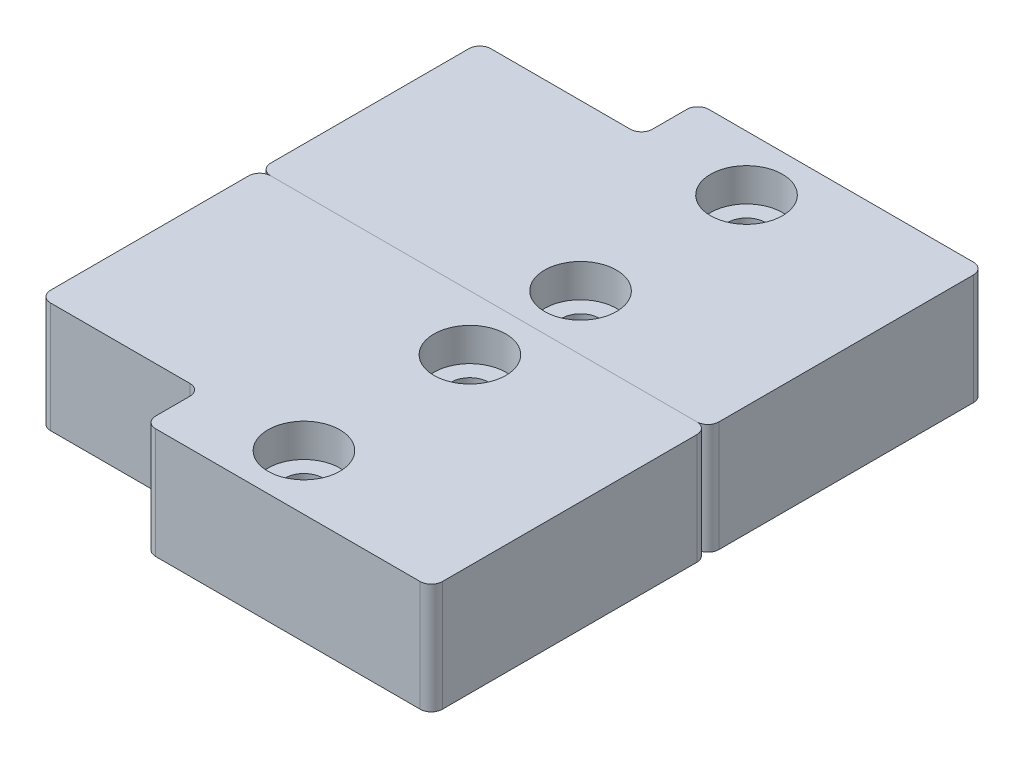
SolidWorks part; units mm, degrees
ref_plane "Front Plane" through (0, 0, 0) normal (0, 0, 1) x (1, 0, 0)
ref_plane "Top Plane" through (0, 0, 0) normal (0, 1, 0) x (1, 0, 0)
ref_plane "Right Plane" through (0, 0, 0) normal (1, 0, 0) x (0, 0, -1)
sketch "Sketch1" plane through (0, 0, 0) normal (0, 1, 0) x (1, 0, 0)
  line L0 (0, 0) -> (40.51, 0)
  line L1 (40.51, 0) -> (40.51, 25)
  line L2 (40.51, 25) -> (14.6, 25)
  line L3 (14.6, 25) -> (14.6, 19.9)
  line L4 (14.6, 19.9) -> (0, 19.9)
  line L5 (0, 19.9) -> (0, 0)
  dimension "D1" = 40.51
  dimension "D2" = 25
  dimension "D3" = 14.6
  dimension "D4" = 5.1
extrude "Boss-Extrude1" add sketch "Sketch1" along normal blind 10
fillet "Fillet1" radius 1 6 edges at (0, 5, -19.9) (14.6, 5, -19.9) (14.6, 5, -25) (40.51, 5, -25) (40.51, 5, 0) (0, 5, 0)
sketch "Sketch2" plane through (0, 10, 0) normal (0, 1, 0) x (1, 0, 0)
  line L0 (24, 25) -> (24, 0) construction
  line L1 (39.51, 25) -> (15.6, 25) construction
  line L2 (1, 0) -> (39.51, 0) construction
  line L3 (40.51, 1) -> (40.51, 24) construction
  line L4 (40.51, 12.5) -> (0, 12.5) construction
  line L5 (0, 18.9) -> (0, 1) construction
  point P12 (24, 20)
  point P13 (24, 5)
  point P14 (24, 12.5)
  dimension "D1" = 16.51
  dimension "D2" = 15
  dimension "D3" = 7.5
hole_wizard "CBORE for M3 SHCS1" positions "Sketch3" profile "Sketch4" counterbore size "M3" standard "ANSI Metric" end condition up to next
sketch "Sketch3" plane through (0, 10, 0) normal (0, 1, 0) x (1, 0, 0)
  point P0 (24, 20)
  point P3 (24, 5)
sketch "Sketch4" plane through (24, 10, -20) normal (1, 0, 0) x (0, 0, 1)
  line L0 (0, 0) -> (0, 10)
  line L1 (0, 10) -> (1.7, 10)
  line L3 (1.7, 10) -> (1.7, 3)
  line L4 (1.7, 3) -> (3.25, 3)
  line L5 (3.25, 3) -> (3.25, 0)
  line L7 (3.25, 0) -> (0, 0)
  line L11 (0, -6.35) -> (0, 107.95) construction
  dimension "Thru Hole Dia." = 3.4
  dimension "Thru Hole Depth" = 10
  dimension "C'Bore Dia." = 6.5
  dimension "C'Bore Depth" = 3
mirror "Mirror1" about plane through (0, 10, 0) normal (0, 0, -1) of bodies 102
